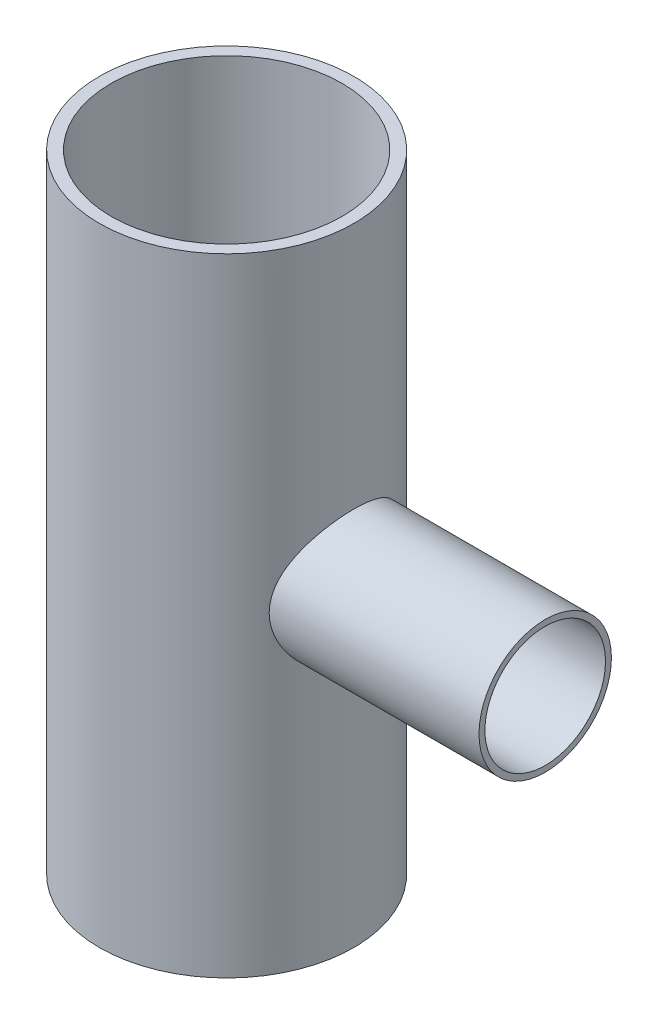
SolidWorks part; units mm, degrees
ref_plane "Front Plane" through (0, 0, 0) normal (0, 0, 1) x (1, 0, 0)
ref_plane "Top Plane" through (0, 0, 0) normal (0, 1, 0) x (1, 0, 0)
ref_plane "Right Plane" through (0, 0, 0) normal (1, 0, 0) x (0, 0, -1)
sketch "Sketch1" plane through (0, 0, 0) normal (0, 1, 0) x (1, 0, 0)
  circle A0 centre (0, 0) radius 161.925
  dimension "D1" = 323.85
extrude "Boss-Extrude1" add sketch "Sketch1" along normal blind 797.56
sketch "Sketch2" plane through (0, 0, 0) normal (1, 0, 0) x (0, 0, -1)
  line L0 (0, 178.1175) -> (0, -178.1175) construction
  line L1 (-161.925, 398.78) -> (161.925, 398.78) construction
  line L2 (-161.925, 797.56) -> (-161.925, 0) construction
  line L3 (161.925, 0) -> (161.925, 797.56) construction
  circle A0 centre (0, 398.78) radius 84.201
  point P4 (0, 0)
  dimension "D1" = 168.402
extrude "Boss-Extrude2" add sketch "Sketch2" along normal blind 405.13
sketch "Sketch3" plane through (0, 0, 0) normal (0, -1, 0) x (1, 0, 0)
  circle A0 centre (0, 0) radius 146.7485
  dimension "D1" = 293.497
extrude "Cut-Extrude1" cut sketch "Sketch3" against normal through all
sketch "Sketch4" plane through (405.13, 0, 0) normal (1, 0, 0) x (0, 0, -1)
  circle A0 centre (0, 398.78) radius 76.6953
  dimension "D1" = 153.3906
extrude "Cut-Extrude2" cut sketch "Sketch4" against normal up to surface (405.13 mm away) up to plane "Right Plane"
